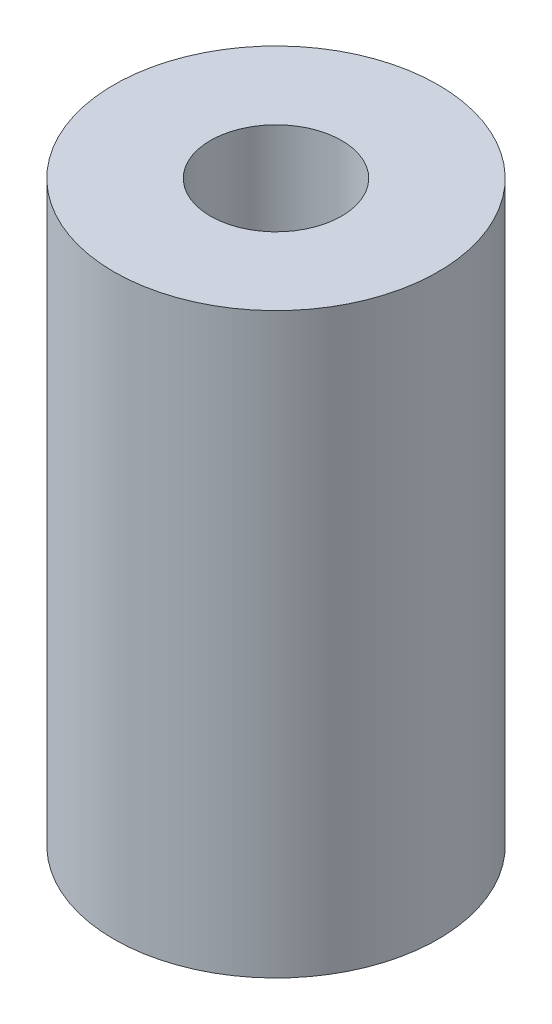
SolidWorks part; units mm, degrees
material "AP"
ref_plane "Front Plane" through (0, 0, 0) normal (0, 0, 1) x (1, 0, 0)
ref_plane "Top Plane" through (0, 0, 0) normal (0, 1, 0) x (1, 0, 0)
ref_plane "Right Plane" through (0, 0, 0) normal (1, 0, 0) x (0, 0, -1)
sketch "Sketch2" plane through (0, 0, 0) normal (0, 1, 0) x (1, 0, 0)
  circle A0 centre (0, 0) radius 42.7355
  circle A1 centre (0, 0) radius 17.2974
  dimension "D1" = 85.471
  dimension "D2" = 34.5948
extrude "Extrude1" add sketch "Sketch2" along normal blind 152.4
